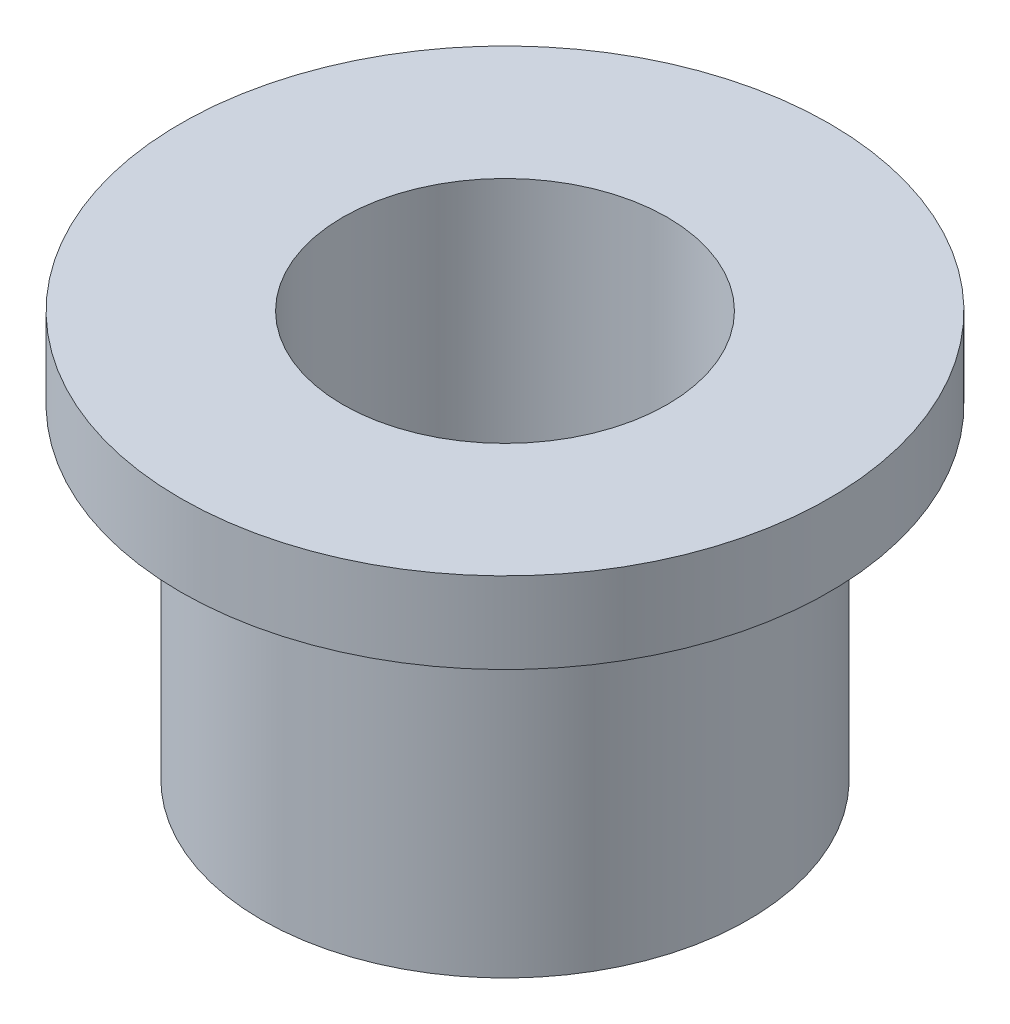
SolidWorks part; units mm, degrees
material "Tin Bearing Bronze"
ref_plane "Front Plane" through (0, 0, 0) normal (0, 0, 1) x (1, 0, 0)
ref_plane "Top Plane" through (0, 0, 0) normal (0, 1, 0) x (1, 0, 0)
ref_plane "Right Plane" through (0, 0, 0) normal (1, 0, 0) x (0, 0, -1)
sketch "Sketch1" plane through (0, 0, 0) normal (1, 0, 0) x (0, 0, -1)
  line L0 (3.175, 0) -> (3.175, 7.9375)
  line L1 (3.175, 7.9375) -> (6.35, 7.9375)
  line L2 (6.35, 7.9375) -> (6.35, 6.35)
  line L3 (6.35, 6.35) -> (4.7625, 6.35)
  line L4 (4.7625, 6.35) -> (4.7625, 0)
  line L5 (4.7625, 0) -> (3.175, 0)
  line L6 (0, 0) -> (0, 9.525) construction
  dimension "D1" = 6.35
  dimension "D2" = 9.525
  dimension "D3" = 6.35
  dimension "D4" = 1.5875
  dimension "D5" = 12.7
revolve "Revolve1" add sketch "Sketch1" angle 360 about L6
